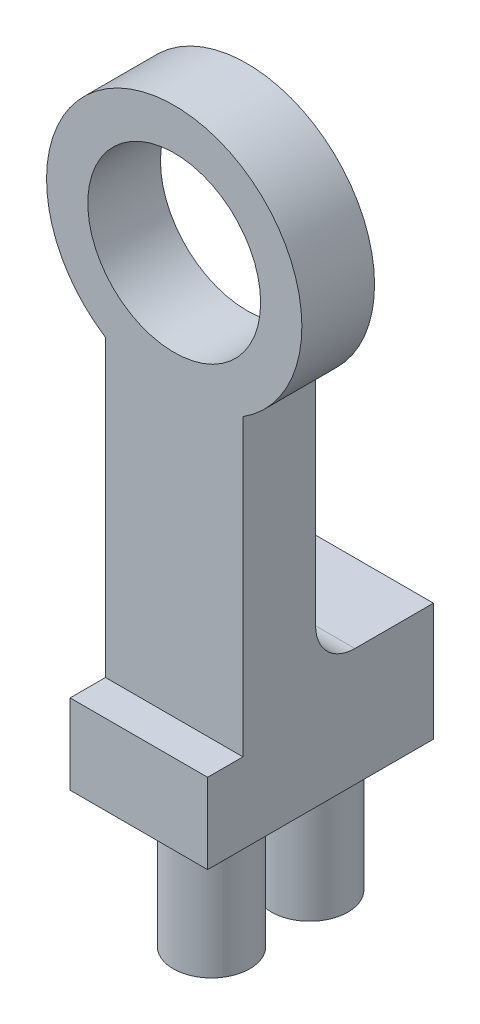
SolidWorks part; units mm, degrees
ref_plane "Front Plane" through (0, 0, 0) normal (0, 0, 1) x (1, 0, 0)
ref_plane "Top Plane" through (0, 0, 0) normal (0, 1, 0) x (1, 0, 0)
ref_plane "Right Plane" through (0, 0, 0) normal (1, 0, 0) x (0, 0, -1)
sketch "Sketch1" plane through (0, 0, 0) normal (0, 0, 1) x (1, 0, 0)
  line L0 (0, 0) -> (0, -35) construction
  line L1 (-3.5, 0) -> (-5.5, 0)
  line L2 (3.5, 0) -> (5.5, 0)
  line L3 (0, -17.5) -> (10.3868, -17.5) construction
  line L5 (-1.5, 3.1623) -> (-1.5, 5.2915)
  line L7 (1.5, 3.1623) -> (1.5, 5.2915)
  line L8 (1.5, -38.1623) -> (1.5, -40.2915)
  line L9 (-1.5, -38.1623) -> (-1.5, -40.2915)
  line L10 (3.5, -35) -> (5.5, -35)
  line L11 (-3.5, -35) -> (-5.5, -35)
  line L13 (-3.5, 0) -> (3.5, 0)
  line L14 (-3.5, 0) -> (-3.5, -35)
  line L15 (-3.5, -35) -> (3.5, -35)
  line L16 (3.5, 0) -> (3.5, -35)
  circle A0 centre (0, 0) radius 2.95
  circle A1 centre (0, 0) radius 6.5
  circle A2 centre (0, 0) radius 3.5
  circle A3 centre (0, 0) radius 5.5
  circle A4 centre (0, -35) radius 5.5
  circle A5 centre (0, -35) radius 3.5
  circle A6 centre (0, -35) radius 6.5
  circle A7 centre (0, -35) radius 2.95
  dimension "D1" = 5.9
  dimension "D2" = 13
  dimension "D3" = 11
  dimension "D4" = 7
  dimension "D5" = 35
extrude "Boss-Extrude1" add sketch "Sketch1" along normal blind 3.7 contours L14 A6 L16 A1 | A3 L16 A1 L14 | L14 A3 L16 A2 | A3 L14 A1 L16 | A6 L14 A4 L16 | A6 L16 A4 L14 | L14 A5 L16 A4 | A4 L11 L14 | A4 L16 L10 | L15 A7 A5 | L15 A7 A5 | L7 A3 L5 A2 | L1 A3 L14 | L16 A3 L2 | L13 A2 A0 | L13 A2 A0 | L8 A5 L9 A4
sketch "Sketch2" plane through (0, 0, 0) normal (1, 0, 0) x (0, 0, -1)
  line L0 (0, 0) -> (0, -24.55) construction
  line L1 (0, -5.4772) -> (0, -29.5228) construction
  line L2 (-3.7, -5.4772) -> (-3.7, -29.5228) construction
  line L3 (-3.7, -24.55) -> (-3.1, -24.55)
  line L4 (-3.7, -24.55) -> (-3.7, -41.5)
  line L5 (-3.7, -41.5) -> (-3.1, -41.5)
  line L6 (-3.1, -24.55) -> (-3.1, -41.5)
  line L7 (-3.7, -41.5) -> (0, -41.5) construction
  dimension "D1" = 24.55
  dimension "D2" = 0.6
extrude "Cut-Extrude1" cut sketch "Sketch2" against normal blind 10 and the other way blind 10
sketch "Sketch3" plane through (0, 0, 0) normal (0, 0, -1) x (-1, 0, 0)
  circle A0 centre (0, -35) radius 2.95
  circle A1 centre (0, -35) radius 1.5
  dimension "D1" = 3
extrude "Boss-Extrude2" add sketch "Sketch3" against normal blind 3.1
sketch "Sketch4" plane through (0, 0, 0) normal (0, 0, -1) x (-1, 0, 0)
  circle A0 centre (0, -35) radius 2.5
  dimension "D1" = 5
extrude "Cut-Extrude2" cut sketch "Sketch4" against normal blind 1.5
sketch "Sketch5" plane through (0, 0, 3.1) normal (0, 0, 1) x (1, 0, 0)
  line L1 (-3.5, -24.55) -> (3.5, -24.55)
  line L2 (-3.5, -24.55) -> (-3.5, -29.5228)
  line L4 (3.5, -24.55) -> (3.5, -29.5228)
  line L5 (-5.5, -35) -> (-3.5, -35)
  line L8 (-1.5, -38.1623) -> (-1.5, -40.2915)
  line L9 (5.5, -35) -> (3.5, -35)
  line L12 (1.5, -38.1623) -> (1.5, -40.2915)
  circle A0 centre (0, -35) radius 1.5
  circle A1 centre (0, -35) radius 6.5
  circle A2 centre (0, -35) radius 3.5
  arc A3 (-5.5, -35) -> (5.5, -35) centre (0, -35) ccw
extrude "Boss-Extrude3" add sketch "Sketch5" along normal blind 0.4
sketch "Sketch6" plane through (0, 0, 3.7) normal (0, 0, 1) x (1, 0, 0)
  line L0 (-1.5, 5.2915) -> (-1.5, 3.1623)
  line L2 (-3.5, -5.4772) -> (-3.5, -24.55)
  line L3 (-3.5, -24.55) -> (3.5, -24.55)
  line L4 (3.5, -5.4772) -> (3.5, -24.55)
  line L5 (1.5, 5.2915) -> (1.5, 3.1623)
  line L6 (3.5, 0) -> (5.5, 0)
  line L7 (-5.5, 0) -> (-3.5, 0)
  circle A0 centre (0, 0) radius 2.95
  arc A1 (3.5, -5.4772) -> (-3.5, -5.4772) centre (0, 0) ccw
  arc A2 (-1.5, 5.2915) -> (-5.5, 0) centre (0, 0) ccw
  arc A3 (-1.5, 3.1623) -> (-3.5, 0) centre (0, 0) ccw
  arc A4 (3.5, 0) -> (1.5, 3.1623) centre (0, 0) ccw
  arc A5 (5.5, 0) -> (1.5, 5.2915) centre (0, 0) ccw
extrude "Boss-Extrude4" add sketch "Sketch6" along normal blind 2.4
sketch "Sketch7" plane through (0, 0, 0) normal (0, 0, 1) x (1, 0, 0)
  line L1 (12.005, 7.8195) -> (-10.0995, 7.8195)
  line L2 (12.005, 7.8195) -> (12.005, -42.7273)
  line L3 (12.005, -42.7273) -> (-10.0995, -42.7273)
  line L4 (-10.0995, 7.8195) -> (-10.0995, -42.7273)
extrude "Cut-Extrude3" cut sketch "Sketch7" along normal blind 0.6
sketch "Sketch8" plane through (0, 0, 3.5) normal (0, 0, 1) x (1, 0, 0)
  line L0 (-1.5, -38.1623) -> (-1.5, -40.2915)
  line L1 (-3.5, -24.55) -> (3.5, -24.55)
  line L2 (-3.5, -24.55) -> (-3.5, -29.5228)
  line L3 (-3.5, -29.5228) -> (3.5, -29.5228)
  line L4 (3.5, -24.55) -> (3.5, -29.5228)
  line L5 (1.5, -38.1623) -> (1.5, -40.2915)
  circle A0 centre (0, -35) radius 6.5
  circle A1 centre (0, -35) radius 1.5
  circle A2 centre (0, -35) radius 5.5
  circle A3 centre (0, -35) radius 3.5
  line M1 (1.5, -40.2915) -> (1.5, -38.1623)
  arc M2 (1.5, -38.1623) -> (3.5, -35) centre (0, -35) ccw
  line M3 (3.5, -35) -> (5.5, -35)
  arc M4 (5.5, -35) -> (1.5, -40.2915) centre (0, -35) cw
  line M5 (-3.5, -24.55) -> (-3.5, -29.5228)
  arc M6 (-3.5, -29.5228) -> (3.5, -29.5228) centre (0, -35) ccw
  line M7 (3.5, -29.5228) -> (3.5, -24.55)
  line M8 (3.5, -24.55) -> (-3.5, -24.55)
  arc M9 (-1.5, -40.2915) -> (-5.5, -35) centre (0, -35) cw
  line M10 (-5.5, -35) -> (-3.5, -35)
  arc M11 (-3.5, -35) -> (-1.5, -38.1623) centre (0, -35) ccw
  line M12 (-1.5, -38.1623) -> (-1.5, -40.2915)
  circle M13 centre (0, -35) radius 1.5
extrude "Boss-Extrude5" add sketch "Sketch8" along normal blind 2.6 contours A0 M7 M8 M5 | A3 M2 M11 M13 | A3 A2 L3 M3 M10 | A2 L3 M4 M9 M6 | A3 A2 M12 M1 | L3 A2 | A2 L3 A0
sketch "Sketch9" plane through (0, 0, 6.1) normal (0, 0, 1) x (1, 0, 0)
  circle A0 centre (0, -35) radius 3.5
  circle A1 centre (0, -35) radius 5.5
extrude "Boss-Extrude6" add sketch "Sketch9" against normal blind 5.5
sketch "Sketch10" plane through (0, 0, 6.1) normal (0, 0, 1) x (1, 0, 0)
  line L1 (-3.5, -31.5) -> (3.5, -31.5)
  line L2 (-3.5, -31.5) -> (-3.5, -38.5)
  line L3 (-3.5, -38.5) -> (3.5, -38.5)
  line L4 (3.5, -31.5) -> (3.5, -38.5)
  line L5 (-3.5, -31.5) -> (3.5, -38.5) construction
  line L6 (-3.5, -38.5) -> (3.5, -31.5) construction
  dimension "D2" = 7
  dimension "D3" = 7
extrude "Cut-Extrude4" cut sketch "Sketch10" against normal blind 5.5
sketch "Sketch11" plane through (0, 0, 6.1) normal (0, 0, 1) x (1, 0, 0)
  line L0 (0, 0) -> (0, -24.55) construction
  line L2 (-9.9851, -24.55) -> (10.8803, -24.55)
  line L3 (-9.9851, -24.55) -> (-9.9851, -42.3593)
  line L4 (-9.9851, -42.3593) -> (10.8803, -42.3593)
  line L5 (10.8803, -24.55) -> (10.8803, -42.3593)
  dimension "D1" = 24.55
extrude "Cut-Extrude5" cut sketch "Sketch11" against normal blind 10
sketch "Sketch12" plane through (0, -24.55, 0) normal (0, -1, 0) x (1, 0, 0)
  line L1 (-3.5, 6.1) -> (3.5, 6.1)
  line L5 (-3.5, 0.6) -> (3.5, 0.6)
  line L6 (-3.5, 0.6) -> (-3.5, -5.4)
  line L7 (-3.5, -5.4) -> (3.5, -5.4)
  line L8 (3.5, 0.6) -> (3.5, -5.4)
  line M1 (-3.5, 0.6) -> (3.5, 0.6)
  dimension "D1" = 6
extrude "Boss-Extrude7" add sketch "Sketch12" against normal blind 6 contours L8 L6 L7 M1
fillet "Fillet1" radius 2 1 edges at (0, -18.55, 0.6)
sketch "Sketch13" plane through (0, -24.55, 0) normal (0, -1, 0) x (1, 0, 0)
  line L0 (3.5, -5.4) -> (3.5, 6.1) construction
  line L1 (3.5, 6.1) -> (-3.5, 6.1) construction
  line L2 (-3.5, -5.4) -> (3.5, -5.4) construction
  line L3 (-3.5, -5.4) -> (-3.5, 6.1) construction
  line L4 (-2, 4.4) -> (2, 4.4) construction
  line L5 (-2, 4.4) -> (-2, -4.6) construction
  line L6 (-2, -4.6) -> (2, -4.6) construction
  line L7 (2, 4.4) -> (2, -4.6) construction
  line L9 (-3.45, 6.1) -> (3.45, 6.1) construction
  line L10 (-3.45, 6.1) -> (-3.45, -5.4) construction
  line L11 (-3.45, -5.4) -> (3.45, -5.4) construction
  line L12 (3.45, 6.1) -> (3.45, -5.4) construction
  circle A0 centre (0, 2.4) radius 1.95
  circle A1 centre (0, -2.6) radius 1.95
  dimension "D1" = 3.9
  dimension "D2" = 3.5
  dimension "D3" = 3.7
  dimension "D5" = 2.8
  dimension "D10" = 6.9
  dimension "D6" = 1.7
  dimension "D7" = 0.8
  dimension "D8" = 1.45
  dimension "D9" = 1.45
  dimension "D11" = 0.05
  dimension "D12" = 11.5
  dimension "D4" = 2
extrude "Boss-Extrude8" add sketch "Sketch13" along normal blind 7
sketch "Sketch14" plane through (0, 0, 6.1) normal (0, 0, 1) x (1, 0, 0)
  line L0 (3.5, -24.55) -> (3.5, -5.4772) construction
  line L1 (-3.5, -5.4772) -> (3.5, -5.4772)
  line L2 (-3.5, -5.4772) -> (-3.5, -20.4772)
  line L3 (-3.5, -20.4772) -> (3.5, -20.4772)
  line L4 (3.5, -5.4772) -> (3.5, -20.4772)
  circle A0 centre (0, 0) radius 6.5
  line M3 (3.5, -24.55) -> (3.5, -5.4772)
  arc M4 (3.5, -5.4772) -> (-3.5, -5.4772) centre (0, 0) ccw
  line M5 (-3.5, -5.4772) -> (-3.5, -24.55)
  circle M6 centre (0, 0) radius 2.95
  line M7 (-3.5, 0) -> (-5.5, 0)
  arc M8 (-5.5, 0) -> (-1.5, 5.2915) centre (0, 0) cw
  line M9 (-1.5, 5.2915) -> (-1.5, 3.1623)
  arc M10 (-1.5, 3.1623) -> (-3.5, 0) centre (0, 0) ccw
  line M11 (1.5, 3.1623) -> (1.5, 5.2915)
  arc M12 (1.5, 5.2915) -> (5.5, 0) centre (0, 0) cw
  line M13 (5.5, 0) -> (3.5, 0)
  arc M14 (3.5, 0) -> (1.5, 3.1623) centre (0, 0) ccw
  dimension "D1" = 15
extrude "Cut-Extrude6" cut sketch "Sketch14" against normal blind 1.5 contours A0 L3 M5 M3 | L1 M4 M6 M14 M11 M12 M13 M10 M7 M8 M9 | L1 A0
sketch "Sketch15" plane through (0, 0, 4.6) normal (0, 0, 1) x (1, 0, 0)
  line L58 (3.5, -20.4772) -> (3.5, -5.4772)
  line L59 (-3.5, -5.4772) -> (-3.5, -20.4772)
  line L60 (-3.5, -20.4772) -> (3.5, -20.4772)
  line L61 (3.5, -20.4772) -> (3.5, -5.4772)
  line L62 (-3.5, -5.4772) -> (-3.5, -20.4772)
  line L63 (-3.5, -20.4772) -> (3.5, -20.4772)
  circle A70 centre (0, 0) radius 2.95
  arc A71 (3.5, -5.4772) -> (-3.5, -5.4772) centre (0, 0) ccw
  arc A72 (3.5, -5.4772) -> (-3.5, -5.4772) centre (0, 0) ccw
  dimension "D1" = 0
extrude "Boss-Extrude9" add sketch "Sketch15" against normal blind 4
sketch "Sketch16" plane through (0, 0, 4.6) normal (0, 0, 1) x (1, 0, 0)
  circle A0 centre (0, 0) radius 4.4
  dimension "D1" = 8.8
extrude "Cut-Extrude7" cut sketch "Sketch16" against normal through all
sketch "Sketch19" plane through (0, 0, 4.6) normal (0, 0, 1) x (1, 0, 0)
  line L1 (-10.7534, 10.1137) -> (10.3761, 10.1137)
  line L2 (-10.7534, 10.1137) -> (-10.7534, -20.4772)
  line L3 (-10.7534, -20.4772) -> (10.3761, -20.4772)
  line L4 (10.3761, 10.1137) -> (10.3761, -20.4772)
extrude "Cut-Extrude10" cut sketch "Sketch19" against normal blind 0.3
